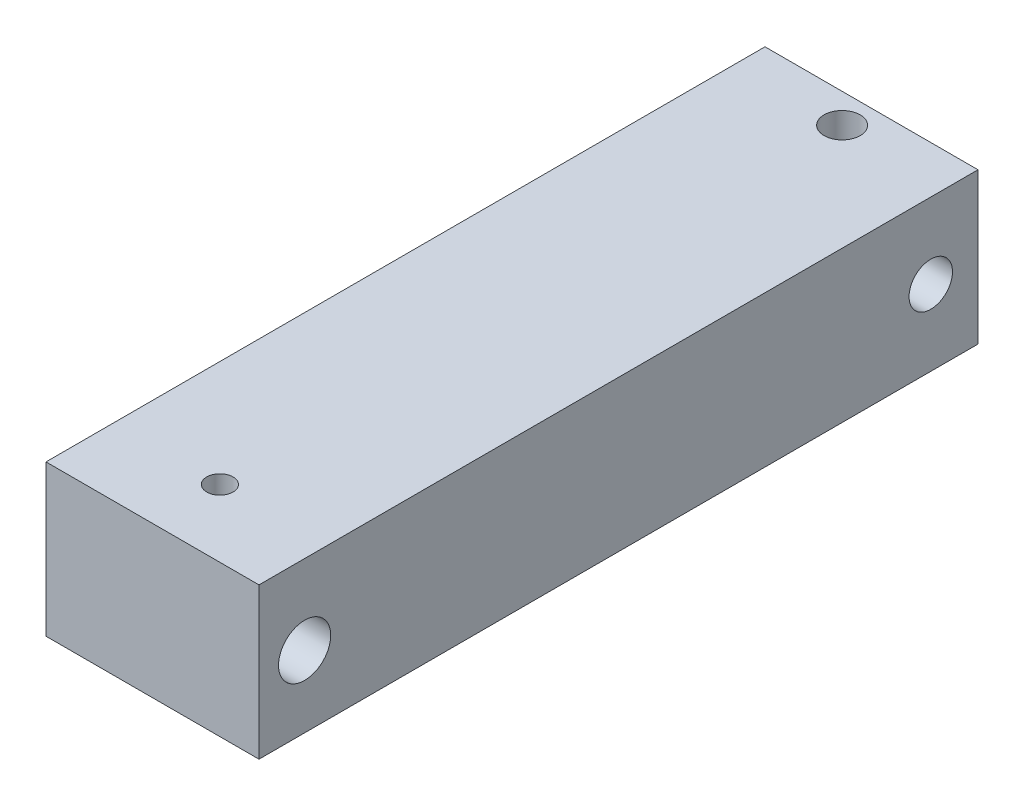
SolidWorks part; units mm, degrees
ref_plane "前视基准面" through (0, 0, 0) normal (0, 0, 1) x (1, 0, 0)
ref_plane "上视基准面" through (0, 0, 0) normal (0, 1, 0) x (1, 0, 0)
ref_plane "右视基准面" through (0, 0, 0) normal (1, 0, 0) x (0, 0, -1)
sketch "草图1" plane through (0, 0, 0) normal (0, 0, 1) x (1, 0, 0)
  line L1 (0, 0) -> (34.6602, 0)
  line L2 (0, 0) -> (0, 24.5704)
  line L3 (0, 24.5704) -> (34.6602, 24.5704)
  line L4 (34.6602, 0) -> (34.6602, 24.5704)
extrude "凸台-拉伸1" add sketch "草图1" along normal blind 117
sketch "草图2" plane through (0, 24.5704, 0) normal (0, 1, 0) x (1, 0, 0)
  circle A0 centre (17.3301, -4.7781) radius 2.9365
  circle A1 centre (17.3301, -106.034) radius 2.1384
extrude "切除-拉伸1" cut sketch "草图2" against normal blind 117
sketch "草图3" plane through (0, 0, 0) normal (-1, 0, 0) x (0, 0, 1)
  circle A0 centre (109.5754, 11.6332) radius 4.2421
extrude "切除-拉伸2" cut sketch "草图3" against normal blind 117
sketch "草图4" plane through (34.6602, 0, 0) normal (1, 0, 0) x (0, 0, -1)
  circle A0 centre (-7.6854, 12.2852) radius 3.5327
extrude "切除-拉伸3" cut sketch "草图4" against normal blind 50
